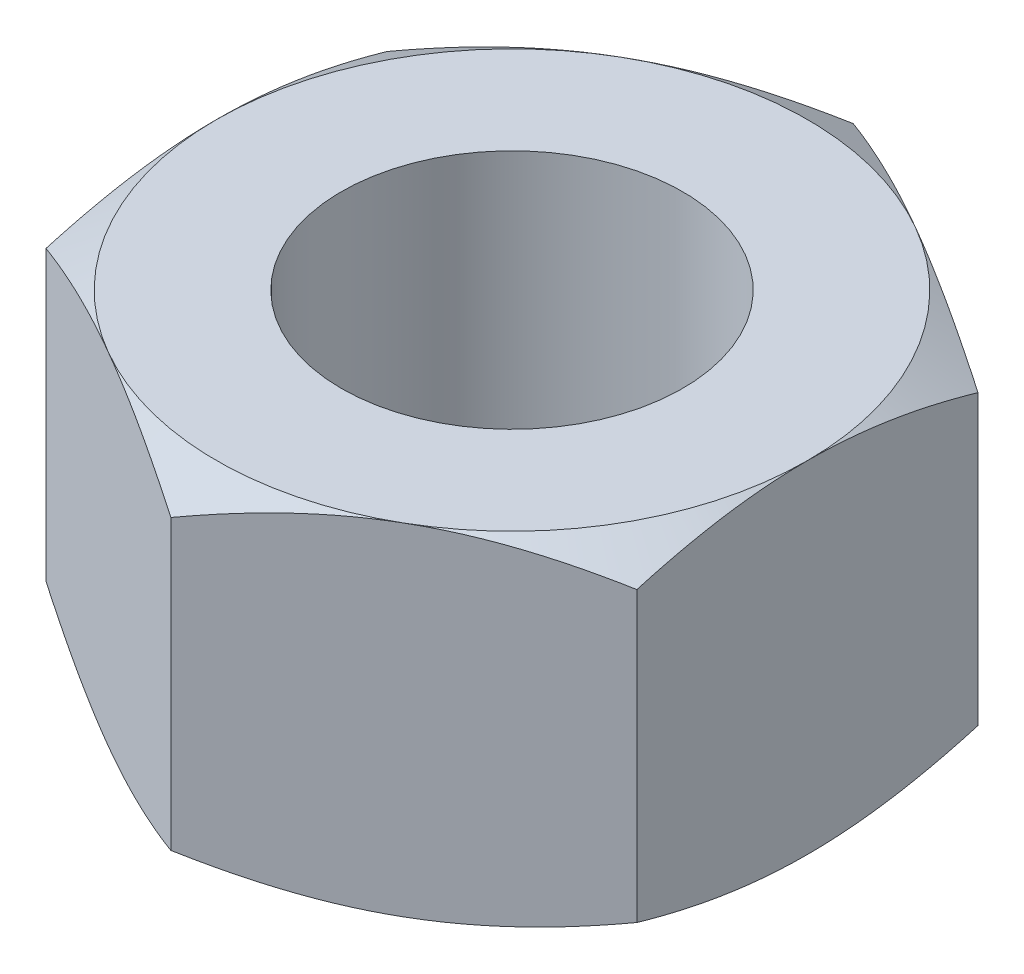
SolidWorks part; units mm, degrees
ref_plane "Front Plane" through (0, 0, 0) normal (0, 0, 1) x (1, 0, 0)
ref_plane "Top Plane" through (0, 0, 0) normal (0, 1, 0) x (1, 0, 0)
ref_plane "Right Plane" through (0, 0, 0) normal (1, 0, 0) x (0, 0, -1)
sketch "Sketch1" plane through (0, 0, 0) normal (0, 1, 0) x (1, 0, 0)
  line L1 (0, -9) -> (7.7942, -4.5)
  line L2 (7.7942, -4.5) -> (7.7942, 4.5)
  line L3 (7.7942, 4.5) -> (0, 9)
  line L4 (0, 9) -> (-7.7942, 4.5)
  line L5 (-7.7942, 4.5) -> (-7.7942, -4.5)
  line L6 (-7.7942, -4.5) -> (0, -9)
  circle A0 centre (0, 0) radius 7.7942 construction
  circle A1 centre (0, 0) radius 4.5
  dimension "D1" = 9
  dimension "D2" = 9
extrude "Boss-Extrude1" add sketch "Sketch1" along normal mid plane 9
sketch "Sketch2" plane through (0, 4.5, 0) normal (0, 1, 0) x (1, 0, 0)
  line L0 (7.7942, -4.5) -> (7.7942, 4.5) construction
  circle A0 centre (0, 0) radius 7.7942
extrude "Cut-Extrude1" cut sketch "Sketch2" against normal blind 10 draft 60 flip side to cut
mirror "Mirror1" about plane through (0, 0, 0) normal (0, 1, 0) of "Cut-Extrude1"
